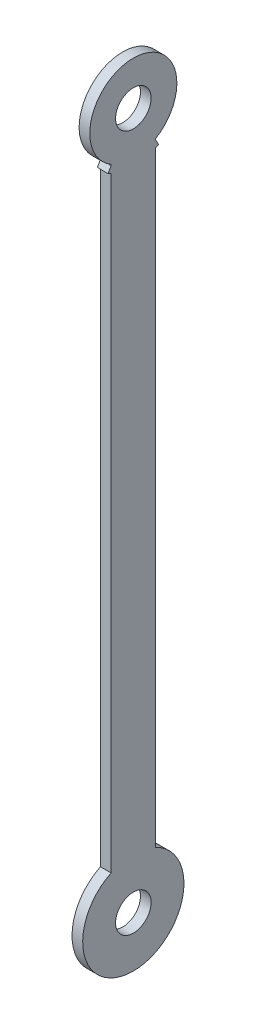
SolidWorks part; units mm, degrees
ref_plane "Front Plane" through (0, 0, 0) normal (0, 0, 1) x (1, 0, 0)
ref_plane "Top Plane" through (0, 0, 0) normal (0, 1, 0) x (1, 0, 0)
ref_plane "Right Plane" through (0, 0, 0) normal (1, 0, 0) x (0, 0, -1)
sketch "Sketch1" plane through (0, 0, 0) normal (1, 0, 0) x (0, 0, -1)
  line L0 (0, -196) -> (0, 196)
  line L1 (12.5, 196) -> (-12.5, 196)
  line L2 (-12.5, 196) -> (-12.5, -196)
  line L3 (-12.5, -196) -> (12.5, -196)
  line L4 (12.5, -196) -> (12.5, 196)
  line L7 (-37.2876, 196) -> (28.5, 196) construction
  line L8 (-12.5, 174.3494) -> (-14.25, 171.3183)
  line L9 (12.5, 174.3494) -> (14.25, 171.3183)
  circle A1 centre (0, -196) radius 28.5
  circle A3 centre (0, 196) radius 24.5
  arc A6 (-14.25, 171.3183) -> (14.25, 171.3183) centre (0, 196) ccw
  point P4 (0, 0)
  point P10 (0, 196)
  dimension "D2" = 49
  dimension "D3" = 57
  dimension "D5" = 57
  dimension "D1" = 392
  dimension "D4" = 25
  dimension "D6" = 60
extrude "Boss-Extrude1" add sketch "Sketch1" along normal mid plane 6
sketch "Sketch2" plane through (3, 0, 0) normal (1, 0, 0) x (0, 0, -1)
  circle A0 centre (0, -196) radius 10
  circle A1 centre (0, 196) radius 10
  dimension "D1" = 20
extrude "Cut-Extrude1" cut sketch "Sketch2" against normal through all
